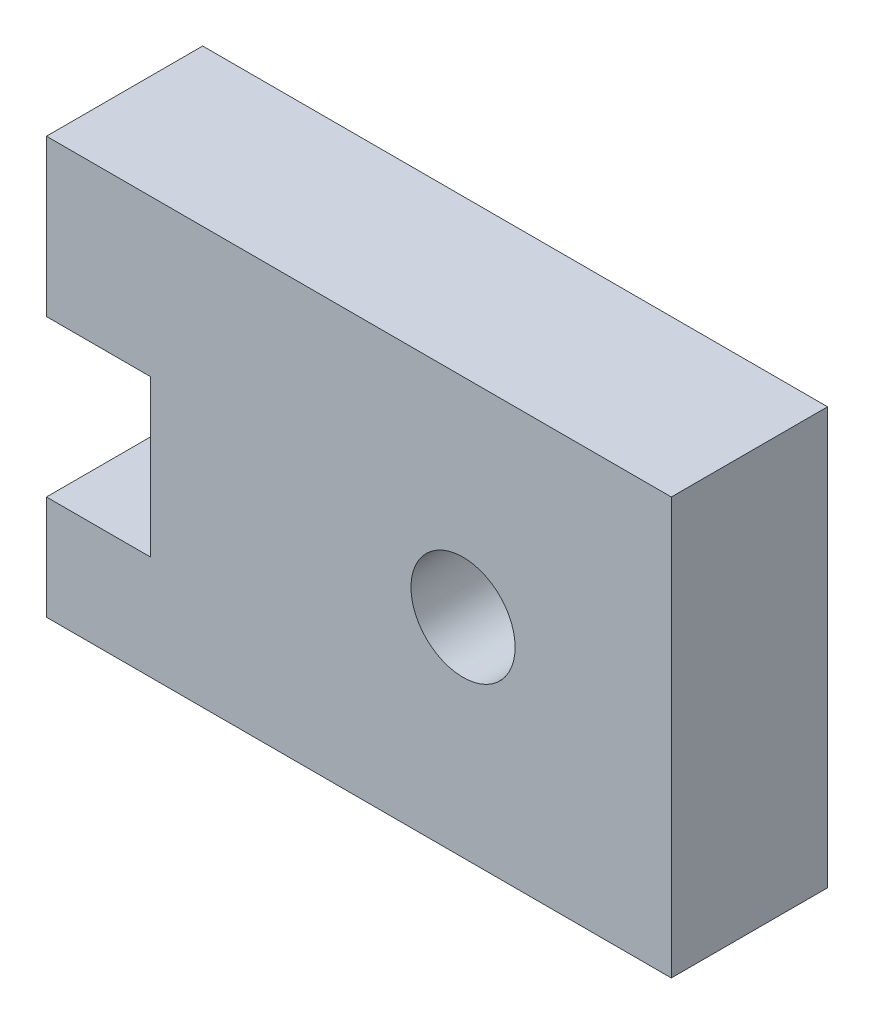
SolidWorks part; units mm, degrees
ref_plane "Front Plane" through (0, 0, 0) normal (0, 0, 1) x (1, 0, 0)
ref_plane "Top Plane" through (0, 0, 0) normal (0, 1, 0) x (1, 0, 0)
ref_plane "Right Plane" through (0, 0, 0) normal (1, 0, 0) x (0, 0, -1)
sketch "Sketch1" plane through (0, 0, 0) normal (0, 0, 1) x (1, 0, 0)
  line L1 (0, 0) -> (19.05, 0)
  line L2 (0, 0) -> (0, 12.7)
  line L3 (0, 12.7) -> (19.05, 12.7)
  line L4 (19.05, 0) -> (19.05, 12.7)
  line L5 (0, 7.9375) -> (3.175, 7.9375)
  line L6 (0, 7.9375) -> (0, 3.175)
  line L7 (0, 3.175) -> (3.175, 3.175)
  line L8 (3.175, 7.9375) -> (3.175, 3.175)
  circle A0 centre (12.7, 6.35) radius 1.5875
  point P12 (0, 0)
  dimension "D5" = 3.175
  dimension "D1" = 12.7
  dimension "D2" = 19.05
  dimension "D3" = 12.7
  dimension "D4" = 6.35
  dimension "D6" = 4.7625
  dimension "D7" = 3.175
  dimension "D8" = 3.175
extrude "Boss-Extrude1" add sketch "Sketch1" along normal blind 4.7625 contours L5 L8 L7 L2 L1 L4 L3 A0
